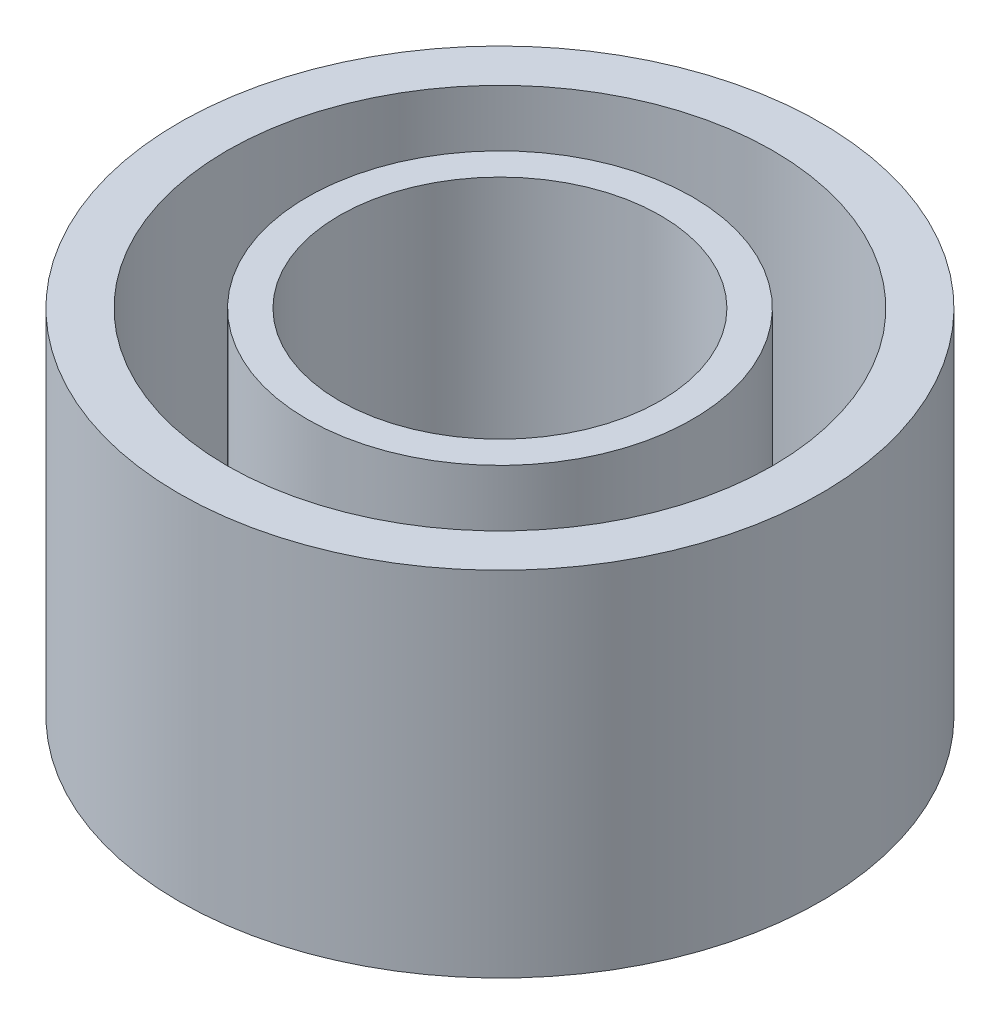
SolidWorks part; units mm, degrees
ref_plane "Ön Düzlem" through (0, 0, 0) normal (0, 0, 1) x (1, 0, 0)
ref_plane "Üst Düzlem" through (0, 0, 0) normal (0, 1, 0) x (1, 0, 0)
ref_plane "Sağ Düzlem" through (0, 0, 0) normal (1, 0, 0) x (0, 0, -1)
sketch "Sketch1" plane through (0, 0, 0) normal (0, 1, 0) x (1, 0, 0)
  circle A0 centre (-45.0433, 0) radius 10
extrude "Boss-Extrude1" add sketch "Sketch1" along normal blind 11
sketch "Sketch2" plane through (0, 11, 0) normal (0, 1, 0) x (1, 0, 0)
  circle A0 centre (-45.0433, 0) radius 6
  circle A1 centre (-45.0433, 0) radius 8.5
  dimension "D1" = 17
  dimension "D2" = 12
extrude "Cut-Extrude1" cut sketch "Sketch2" against normal blind 10
sketch "Sketch3" plane through (0, 11, 0) normal (0, 1, 0) x (1, 0, 0)
  circle A0 centre (-45.0433, 0) radius 5
extrude "Cut-Extrude2" cut sketch "Sketch3" against normal blind 10
